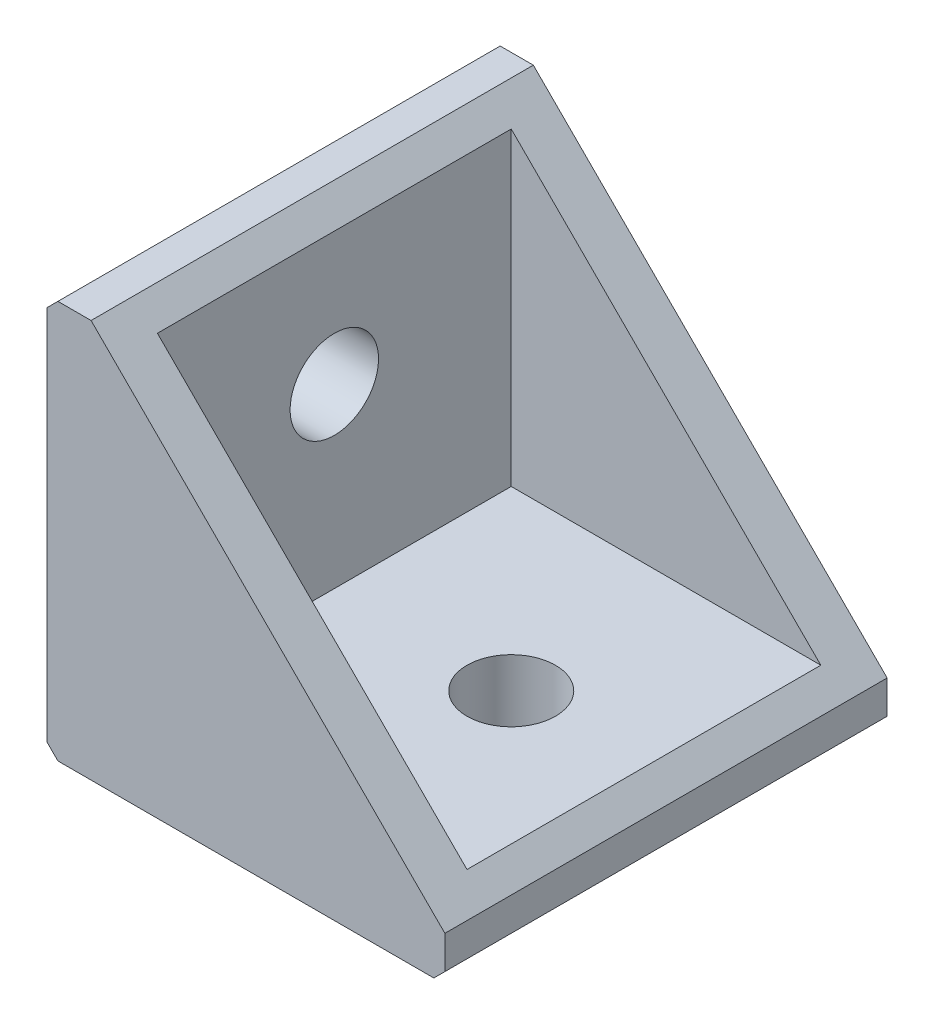
SolidWorks part; units mm, degrees
ref_plane "Plan de face" through (0, 0, 0) normal (0, 0, 1) x (1, 0, 0)
ref_plane "Plan de dessus" through (0, 0, 0) normal (0, 1, 0) x (1, 0, 0)
ref_plane "Plan de droite" through (0, 0, 0) normal (1, 0, 0) x (0, 0, -1)
sketch "Esquisse1" plane through (0, 0, 0) normal (0, 0, 1) x (1, 0, 0)
  line L1 (0, 0) -> (18, 0)
  line L2 (0, 0) -> (0, 18)
  line L3 (0, 18) -> (18, 18)
  line L4 (18, 0) -> (18, 18)
  dimension "D1" = 18
  dimension "D2" = 18
extrude "Boss.-Extru.1" add sketch "Esquisse1" along normal blind 20
sketch "Esquisse2" plane through (0, 0, 20) normal (0, 0, 1) x (1, 0, 0)
  line L0 (18, 18) -> (2, 18)
  line L1 (18, 18) -> (0, 18) construction
  line L2 (2, 18) -> (18, 2)
  line L3 (18, 0) -> (18, 18) construction
  line L4 (18, 2) -> (18, 18)
  dimension "D1" = 16
  dimension "D2" = 16
extrude "Enlèv. mat.-Extru.1" cut sketch "Esquisse2" against normal blind 20
sketch "Esquisse3" plane through (0, 0, 20) normal (0, 0, 1) x (1, 0, 0)
  line L3 (3, 17) -> (3, 3)
  line L4 (3, 3) -> (17, 3)
  line L5 (17, 3) -> (3, 17)
  line L6 (0, 18) -> (0, 0) construction
  line L7 (0, 0) -> (18, 0) construction
  dimension "D1" = 3
  dimension "D2" = 3
extrude "Enlèv. mat.-Extru.2" cut sketch "Esquisse3" against normal blind 16 from offset 2 offset against normal yes
chamfer "Chanfrein1" distance 0.5 angle 45 3 edges at (0, 0, 10) (18, 0, 10) (0, 18, 10)
sketch "Esquisse4" plane through (3, 0, 0) normal (1, 0, 0) x (0, 0, -1)
  line L0 (-2, 17) -> (-2, 3) construction
  line L1 (0, 18) -> (-20, 18) construction
  circle A0 centre (-10, 11) radius 2
  dimension "D1" = 4
  dimension "D2" = 8
  dimension "D3" = 7
extrude "Enlèv. mat.-Extru.3" cut sketch "Esquisse4" against normal through all
sketch "Esquisse5" plane through (0, 3, 0) normal (0, 1, 0) x (1, 0, 0)
  line L0 (18, 0) -> (18, -20) construction
  line L1 (3, -2) -> (17, -2) construction
  circle A0 centre (11, -10) radius 2
  dimension "D1" = 4
  dimension "D2" = 7
  dimension "D3" = 8
extrude "Enlèv. mat.-Extru.4" cut sketch "Esquisse5" against normal through all
